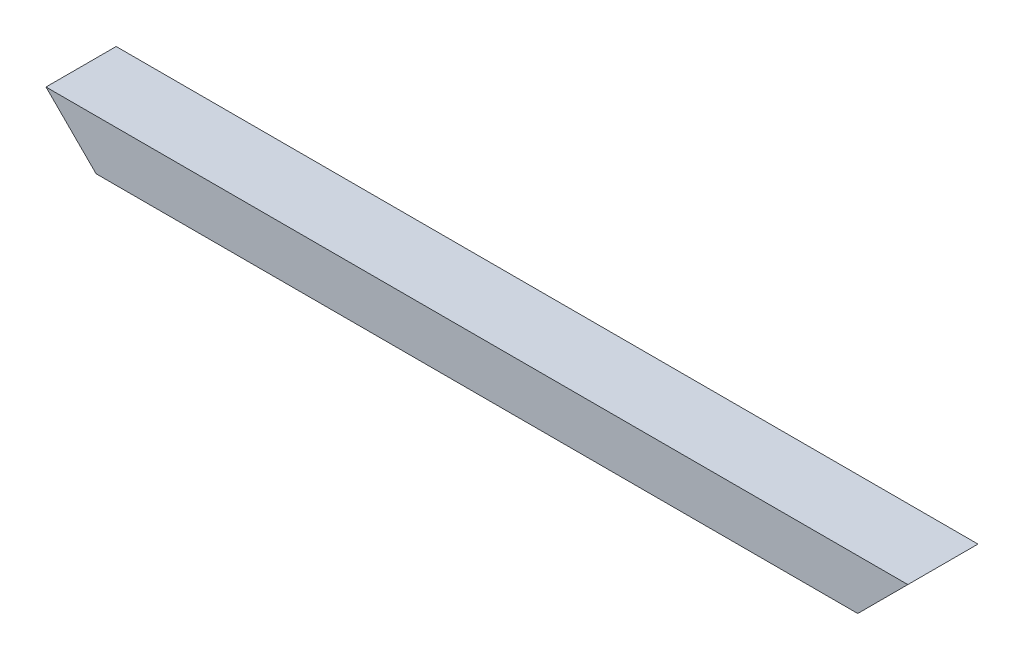
SolidWorks part; units mm, degrees
material "1023 Carbon Steel Sheet (SS)"
ref_plane "Front Plane" through (0, 0, 0) normal (0, 0, 1) x (1, 0, 0)
ref_plane "Top Plane" through (0, 0, 0) normal (0, 1, 0) x (1, 0, 0)
ref_plane "Right Plane" through (0, 0, 0) normal (1, 0, 0) x (0, 0, -1)
sketch "Sketch2" plane through (0, 0, 0) normal (0, 0, 1) x (1, 0, 0)
  line L0 (0, 0) -> (965.2, 0)
  line L1 (965.2, 0) -> (1028.7, 63.5)
  line L2 (1028.7, 63.5) -> (-63.5, 63.5)
  line L3 (-63.5, 63.5) -> (0, 0)
  dimension "D1" = 135
  dimension "D2" = 135
  dimension "D3" = 965.2
  dimension "D4" = 63.5
extrude "Boss-Extrude1" add sketch "Sketch2" along normal blind 88.9
